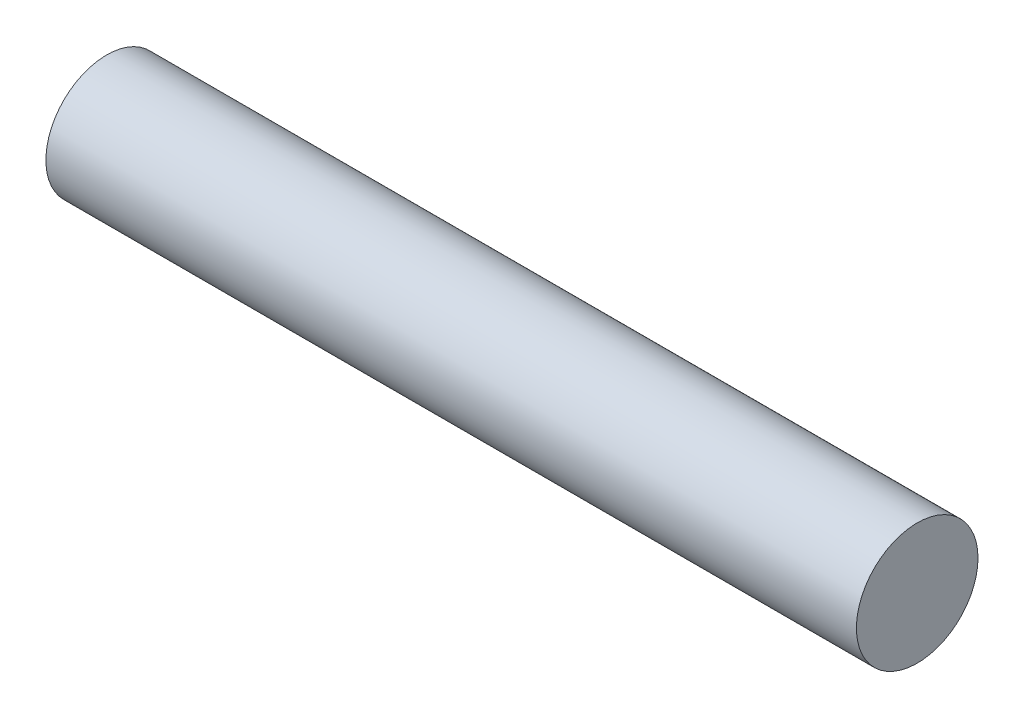
SolidWorks part; units mm, degrees
ref_plane "Front Plane" through (0, 0, 0) normal (0, 0, 1) x (1, 0, 0)
ref_plane "Top Plane" through (0, 0, 0) normal (0, 1, 0) x (1, 0, 0)
ref_plane "Right Plane" through (0, 0, 0) normal (1, 0, 0) x (0, 0, -1)
sketch "Sketch1" plane through (0, 0, 0) normal (1, 0, 0) x (0, 0, -1)
  circle A0 centre (0, 0) radius 4.5
  dimension "D1" = 9
extrude "Boss-Extrude1" add sketch "Sketch1" along normal mid plane 60
